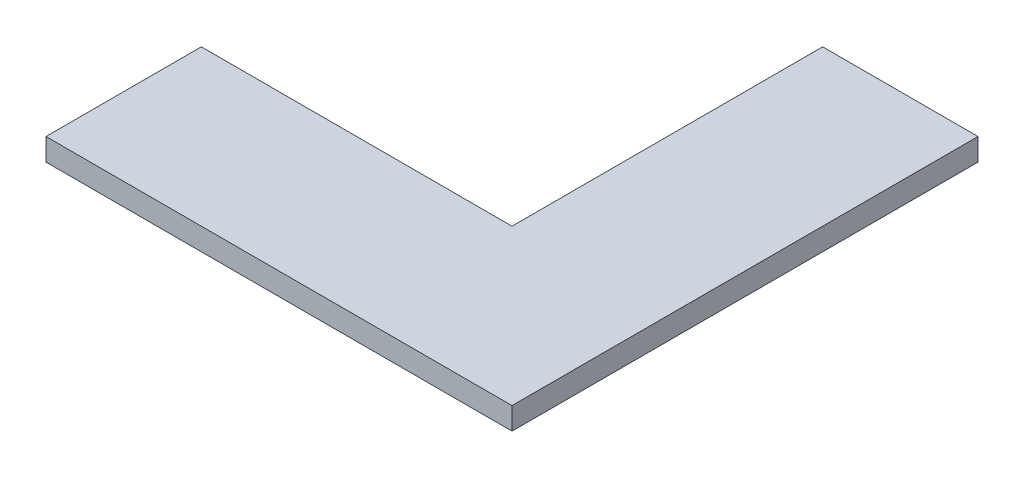
SolidWorks part; units mm, degrees
ref_plane "Front Plane" through (0, 0, 0) normal (0, 0, 1) x (1, 0, 0)
ref_plane "Top Plane" through (0, 0, 0) normal (0, 1, 0) x (1, 0, 0)
ref_plane "Right Plane" through (0, 0, 0) normal (1, 0, 0) x (0, 0, -1)
sketch "Sketch1" plane through (0, 0, 0) normal (0, 1, 0) x (1, 0, 0)
  line L0 (-105, 105) -> (105, -105) construction
  line L1 (-105, 105) -> (105, 105) construction
  line L2 (-105, 105) -> (-105, -105) construction
  line L3 (-105, -105) -> (105, -105) construction
  line L4 (105, 105) -> (105, -105) construction
  line L5 (35, 105) -> (105, 105)
  line L6 (105, 105) -> (105, -105)
  line L7 (105, -105) -> (-105, -105)
  line L8 (-105, -105) -> (-105, -35)
  line L9 (-105, -35) -> (35, -35)
  line L10 (35, -35) -> (35, 105)
  dimension "D1" = 210
  dimension "D2" = 210
  dimension "D3" = 70
  dimension "D4" = 70
extrude "Boss-Extrude1" add sketch "Sketch1" along normal blind 10
